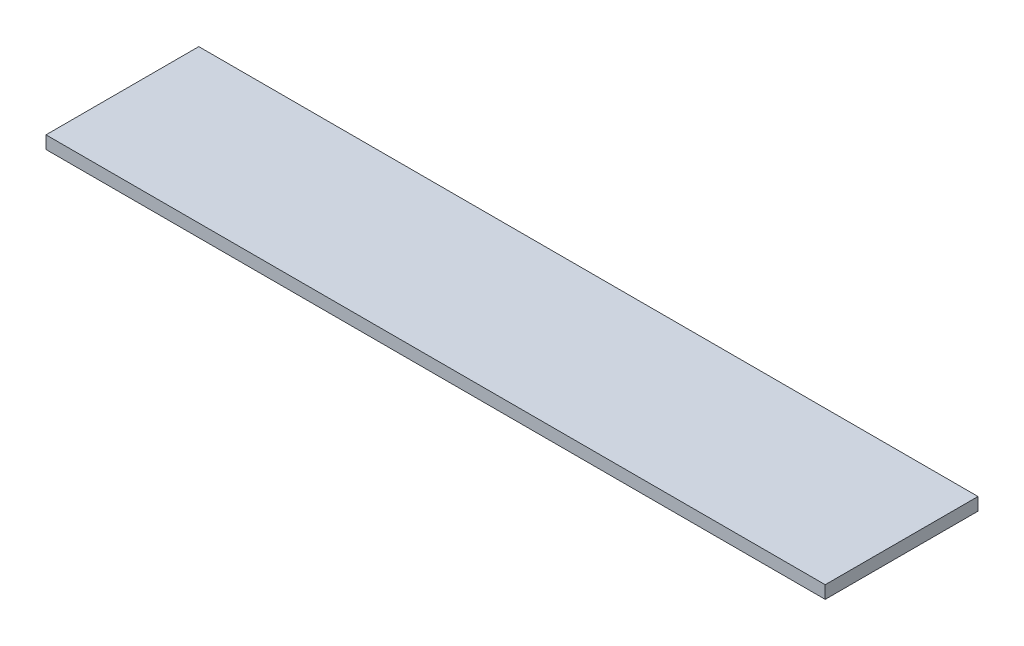
SolidWorks part; units mm, degrees
material "Pine"
ref_plane "Front Plane" through (0, 0, 0) normal (0, 0, 1) x (1, 0, 0)
ref_plane "Top Plane" through (0, 0, 0) normal (0, 1, 0) x (1, 0, 0)
ref_plane "Right Plane" through (0, 0, 0) normal (1, 0, 0) x (0, 0, -1)
sketch "Sketch1" plane through (0, 0, 0) normal (0, 1, 0) x (1, 0, 0)
  line L1 (-388.62, 76.2) -> (388.62, 76.2)
  line L2 (-388.62, 76.2) -> (-388.62, -76.2)
  line L3 (-388.62, -76.2) -> (388.62, -76.2)
  line L4 (388.62, 76.2) -> (388.62, -76.2)
  line L5 (-388.62, 76.2) -> (388.62, -76.2) construction
  line L6 (-388.62, -76.2) -> (388.62, 76.2) construction
  point P0 (0, 0)
  dimension "D1" = 152.4
  dimension "D2" = 777.24
extrude "Boss-Extrude1" add sketch "Sketch1" along normal blind 12.7 contours L1 L4 L3 L2
